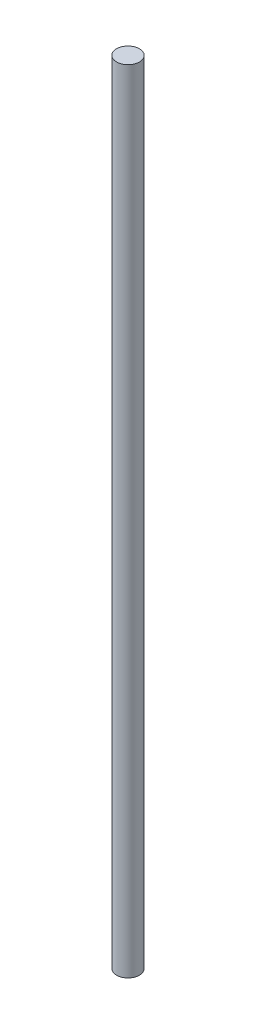
SolidWorks part; units mm, degrees
ref_plane "Front Plane" through (0, 0, 0) normal (0, 0, 1) x (1, 0, 0)
ref_plane "Top Plane" through (0, 0, 0) normal (0, 1, 0) x (1, 0, 0)
ref_plane "Right Plane" through (0, 0, 0) normal (1, 0, 0) x (0, 0, -1)
sketch "Sketch1" plane through (0, 0, 0) normal (0, 1, 0) x (1, 0, 0)
  circle A0 centre (0, 0) radius 0.94
  dimension "D1" = 1.88
extrude "Rod" add sketch "Sketch1" along normal mid plane 65
sketch "Sketch2" plane through (0, 0, 0) normal (0, 1, 0) x (1, 0, 0)
  line L1 (-0.94, -0.94) -> (0.94, -0.94)
  line L2 (-0.94, -0.94) -> (-0.94, 0.94)
  line L3 (-0.94, 0.94) -> (0.94, 0.94)
  line L4 (0.94, -0.94) -> (0.94, 0.94)
  line L5 (-0.94, -0.94) -> (0.94, 0.94) construction
  line L6 (-0.94, 0.94) -> (0.94, -0.94) construction
  point P0 (0, 0)
  dimension "D1" = 1.88
extrude "Cube" [suppressed] add sketch "Sketch2" along normal mid plane 1.88 separate body
